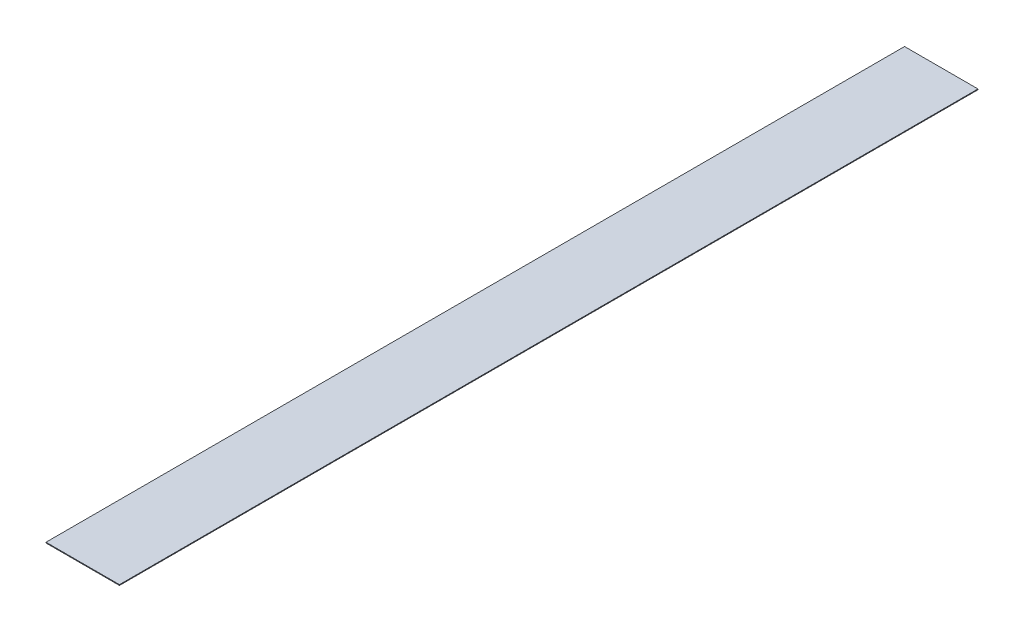
SolidWorks part; units mm, degrees
ref_plane "Front Plane" through (0, 0, 0) normal (0, 0, 1) x (1, 0, 0)
ref_plane "Top Plane" through (0, 0, 0) normal (0, 1, 0) x (1, 0, 0)
ref_plane "Right Plane" through (0, 0, 0) normal (1, 0, 0) x (0, 0, -1)
sketch "Sketch1" plane through (0, 0, 0) normal (0, 1, 0) x (1, 0, 0)
  line L1 (-25.4, 0) -> (25.4, 0)
  line L2 (-25.4, 0) -> (-25.4, 593.725)
  line L3 (-25.4, 593.725) -> (25.4, 593.725)
  line L4 (25.4, 0) -> (25.4, 593.725)
  dimension "D1" = 50.8
  dimension "D2" = 593.725
extrude "Boss-Extrude1" add sketch "Sketch1" along normal blind 0.508
